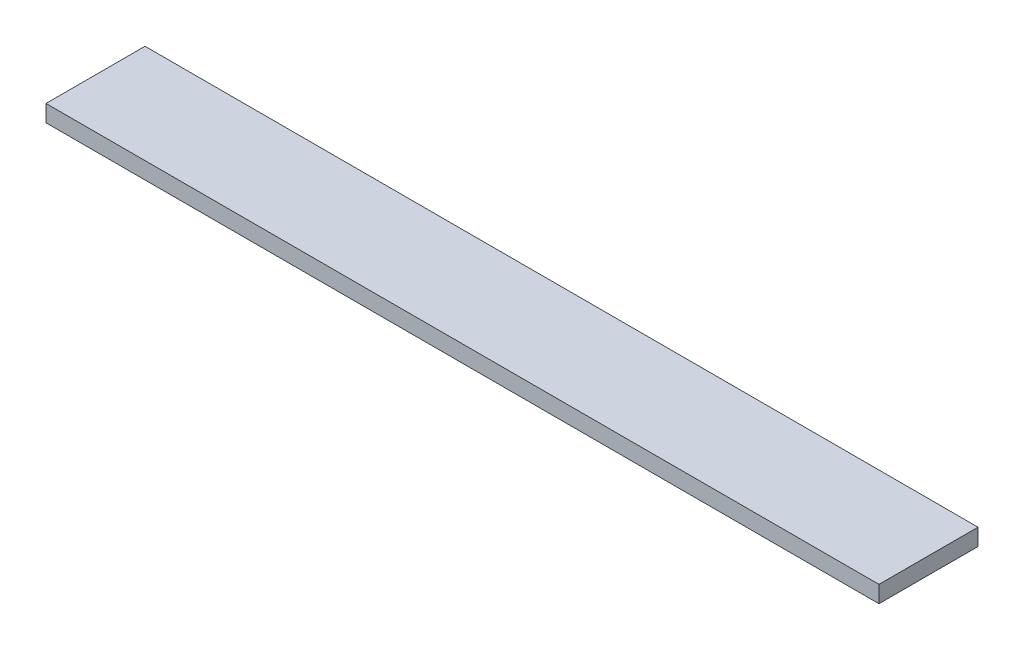
SolidWorks part; units mm, degrees
material "Teak"
ref_plane "Front Plane" through (0, 0, 0) normal (0, 0, 1) x (1, 0, 0)
ref_plane "Top Plane" through (0, 0, 0) normal (0, 1, 0) x (1, 0, 0)
ref_plane "Right Plane" through (0, 0, 0) normal (1, 0, 0) x (0, 0, -1)
sketch "Sketch1" plane through (0, 0, 0) normal (0, 1, 0) x (1, 0, 0)
  line L1 (-123.011, 24.2309) -> (373.3567, 24.2309)
  line L2 (-123.011, 24.2309) -> (-123.011, -34.7831)
  line L3 (-123.011, -34.7831) -> (373.3567, -34.7831)
  line L4 (373.3567, 24.2309) -> (373.3567, -34.7831)
extrude "Extrude1" add sketch "Sketch1" against normal blind 10
